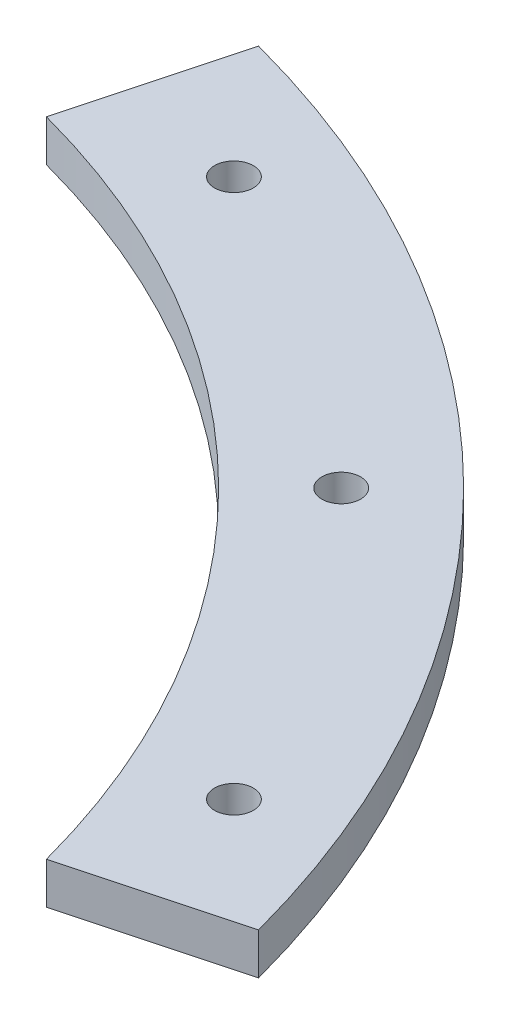
SolidWorks part; units mm, degrees
ref_plane "Front" through (0, 0, 0) normal (0, 0, 1) x (1, 0, 0)
ref_plane "Top" through (0, 0, 0) normal (0, 1, 0) x (1, 0, 0)
ref_plane "Right" through (0, 0, 0) normal (1, 0, 0) x (0, 0, -1)
sketch "Sketch1" plane through (0, 0, 0) normal (0, 1, 0) x (1, 0, 0)
  line L0 (20.5438, 76.6704) -> (0, 0)
  line L1 (0, 0) -> (76.6704, 20.5438)
  line L2 (0, 0) -> (51.6365, 51.6365) construction
  circle A0 centre (0, 0) radius 79.375
  circle A1 centre (0, 0) radius 73.025 construction
  circle A2 centre (0, 0) radius 66.675
  circle A3 centre (0, 73.025) radius 1.4224
  circle A4 centre (27.9455, 67.4663) radius 1.4224
  circle A5 centre (51.6365, 51.6365) radius 1.4224
  circle A6 centre (67.4663, 27.9455) radius 1.4224
  circle A7 centre (73.025, 0) radius 1.4224
  circle A8 centre (67.4663, -27.9455) radius 1.4224
  circle A9 centre (51.6365, -51.6365) radius 1.4224
  circle A10 centre (27.9455, -67.4663) radius 1.4224
  circle A11 centre (0, -73.025) radius 1.4224
  circle A12 centre (-27.9455, -67.4663) radius 1.4224
  circle A13 centre (-51.6365, -51.6365) radius 1.4224
  circle A14 centre (-67.4663, -27.9455) radius 1.4224
  circle A15 centre (-73.025, 0) radius 1.4224
  circle A16 centre (-67.4663, 27.9455) radius 1.4224
  circle A17 centre (-51.6365, 51.6365) radius 1.4224
  circle A18 centre (-27.9455, 67.4663) radius 1.4224
  point P40 (0, 0)
  dimension "D1" = 158.75
  dimension "D2" = 133.35
  dimension "D3" = 146.05
  dimension "D4" = 2.8448
  dimension "D6" = 60
  dimension "D7" = 30
  dimension "D5" = 16
extrude "Boss-Extrude1" add sketch "Sketch1" along normal blind 3.048 contours A2 L1 A0 L0 A7 A6 A5 A4 A3
